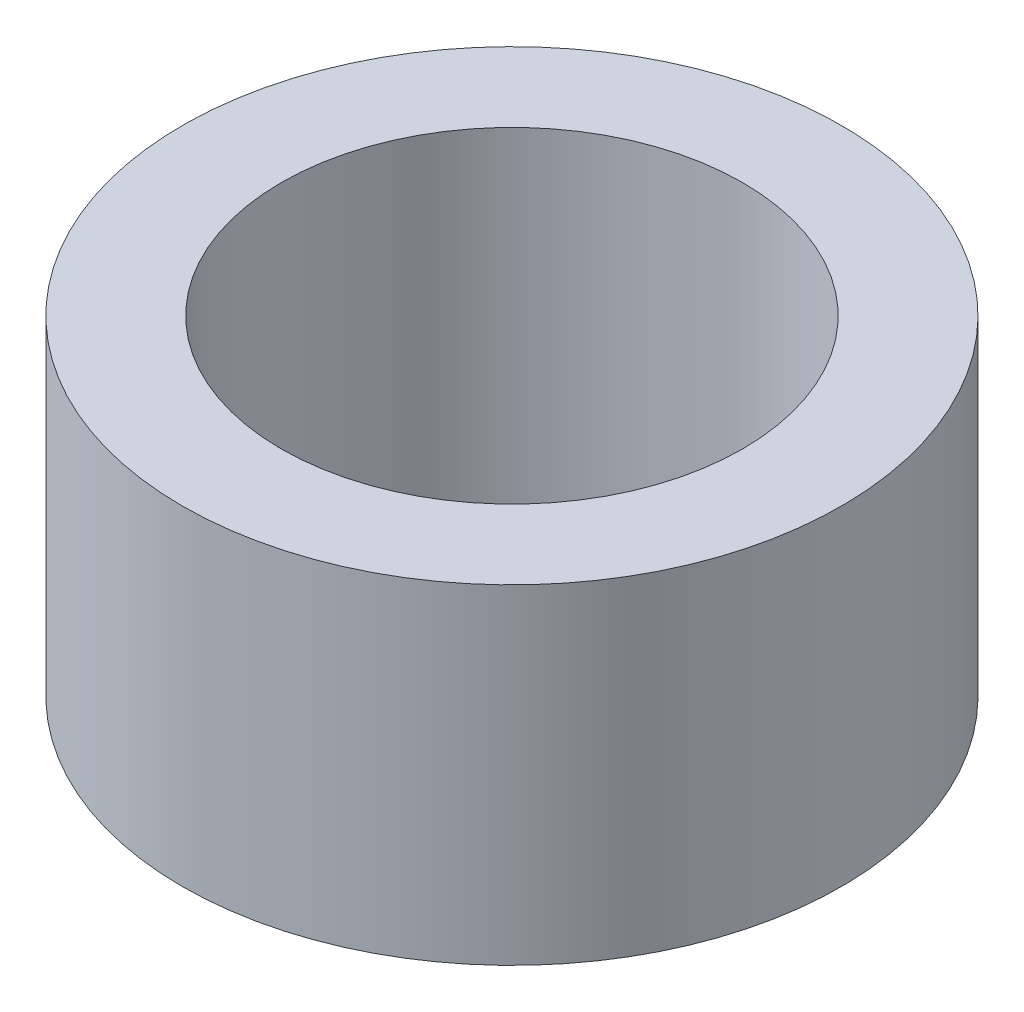
SolidWorks part; units mm, degrees
ref_plane "Front Plane" through (0, 0, 0) normal (0, 0, 1) x (1, 0, 0)
ref_plane "Top Plane" through (0, 0, 0) normal (0, 1, 0) x (1, 0, 0)
ref_plane "Right Plane" through (0, 0, 0) normal (1, 0, 0) x (0, 0, -1)
sketch "Sketch1" plane through (0, 0, 0) normal (0, 1, 0) x (1, 0, 0)
  circle A0 centre (0, 0) radius 2.1
  circle A1 centre (0, 0) radius 3
  dimension "D1" = 6
  dimension "D2" = 4.2
extrude "Boss-Extrude1" add sketch "Sketch1" along normal blind 3
